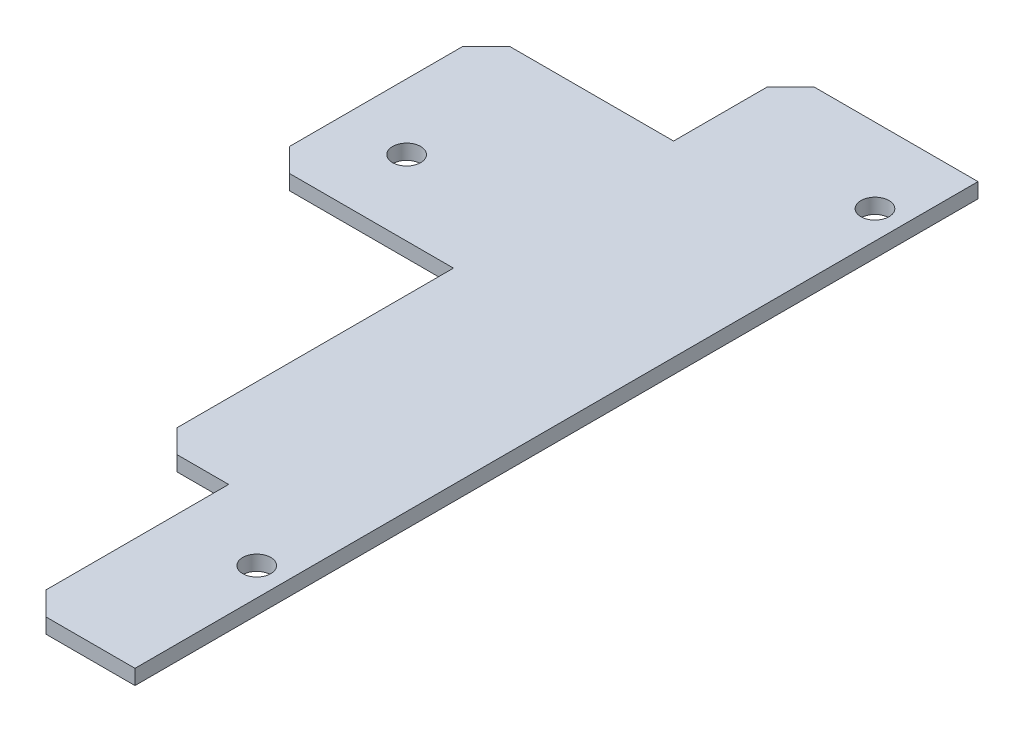
SolidWorks part; units mm, degrees
material "PE High Density"
ref_plane "Front Plane" through (0, 0, 0) normal (0, 0, 1) x (1, 0, 0)
ref_plane "Top Plane" through (0, 0, 0) normal (0, 1, 0) x (1, 0, 0)
ref_plane "Right Plane" through (0, 0, 0) normal (1, 0, 0) x (0, 0, -1)
sketch "Sketch1" plane through (0, 0, 0) normal (0, 1, 0) x (1, 0, 0)
  line L0 (0, -32) -> (8, -32)
  line L1 (-20, 36) -> (20, 36)
  line L2 (-20, 36) -> (-20, 0)
  line L3 (-20, 0) -> (0, 0)
  line L4 (20, 36) -> (20, -54)
  line L5 (8, -32) -> (8, -54)
  line L7 (20, -54) -> (8, -54)
  line L8 (0, 0) -> (0, -32)
  dimension "D1" = 90
  dimension "D2" = 40
  dimension "D3" = 36
  dimension "D4" = 12
  dimension "D5" = 20
  dimension "D6" = 22
extrude "Extrude1" add sketch "Sketch1" along normal blind 1.6
sketch "Sketch2" plane through (0, 1.6, 0) normal (0, 1, 0) x (1, 0, 0)
  line L0 (20, -54) -> (20, 36) construction
  line L1 (20, 36) -> (-20, 36) construction
  line L2 (0, 0) -> (0, -32) construction
  line L3 (-20, 36) -> (0, 36)
  line L4 (-20, 36) -> (-20, 23.5)
  line L5 (-20, 23.5) -> (0, 23.5)
  line L6 (0, 36) -> (0, 23.5)
  circle A0 centre (17, 28) radius 1.5
  circle A1 centre (-13, 8) radius 1.5
  circle A2 centre (17, -38) radius 1.5
  dimension "D2" = 3
  dimension "D4" = 3
  dimension "D5" = 3
  dimension "D1" = 3
  dimension "D3" = 8
  dimension "D6" = 20
  dimension "D7" = 30
  dimension "D8" = 66
  dimension "D9" = 3
  dimension "D11" = 12.5
extrude "Cut-Extrude1" cut sketch "Sketch2" against normal blind 1.6
chamfer "Chamfer1" distance 2.5 angle 45 5 edges at (0, 0.8, 32) (-20, 0.8, 0) (8, 0.8, 54) (0, 0.8, -36) (-20, 0.8, -23.5)
